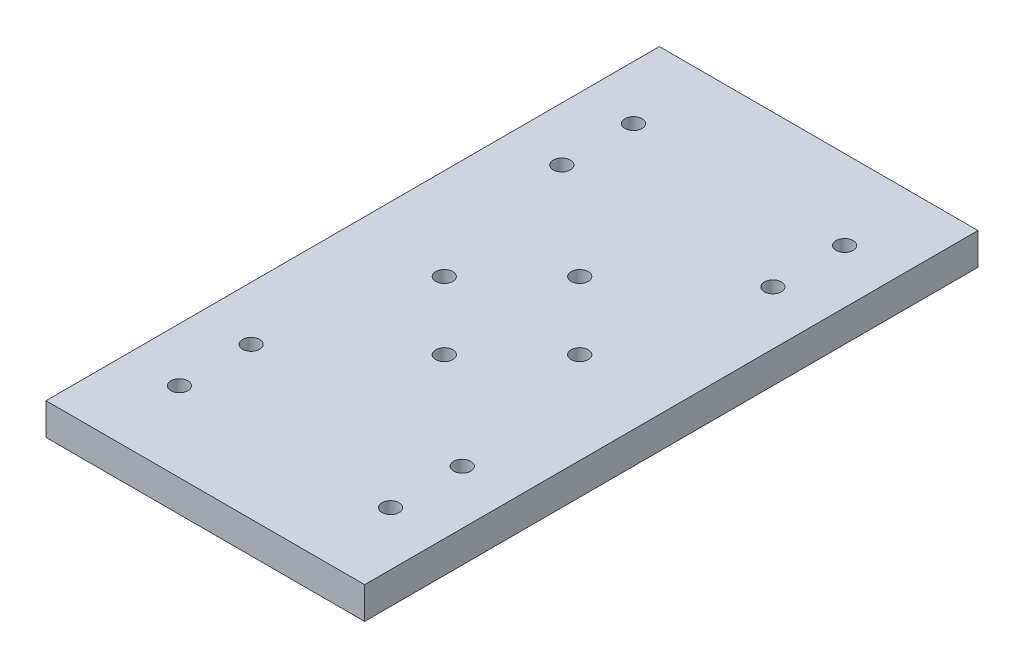
SolidWorks part; units mm, degrees
material "1060 Alloy"
ref_plane "Front" through (0, 0, 0) normal (0, 0, 1) x (1, 0, 0)
ref_plane "Top" through (0, 0, 0) normal (0, 1, 0) x (1, 0, 0)
ref_plane "Right" through (0, 0, 0) normal (1, 0, 0) x (0, 0, -1)
sketch "Sketch1" plane through (0, 0, 0) normal (0, 1, 0) x (1, 0, 0)
  line L0 (-83, 40) -> (-83, -40)
  line L1 (0, 0) -> (-83, 0)
  line L2 (0, 0) -> (0, 68.9891)
  line L3 (-40, 91.6515) -> (40, 91.6515)
  line L4 (-40, 91.6515) -> (-40, -91.6515)
  line L5 (-40, -91.6515) -> (40, -91.6515)
  line L6 (40, -91.6515) -> (40, 91.6515)
  line L7 (-40, 80.5) -> (40, 80.5)
  line L8 (-40, -80.5) -> (40, -80.5)
  circle A0 centre (0, 0) radius 92.1358
  circle A1 centre (0, 0) radius 100
  point P10 (-40, 80.5)
  dimension "D1" = 40
  dimension "D4" = 200
  dimension "D5" = 80
  dimension "D6" = 80.5
  dimension "D2" = 80
  dimension "D3" = 83
extrude "Boss-Extrude1" add sketch "Sketch1" along normal blind 8
hole_wizard "M4 Clearance Hole1" positions "Sketch3" profile "Sketch2" hole size "M4" standard "ISO" end condition through all
sketch "Sketch3" plane through (0, 8, 0) normal (0, 1, 0) x (1, 0, 0)
  line L0 (0, 0) -> (-28.0852, 0)
  line L1 (40, -80.5) -> (40, 80.5) construction
  line L2 (-40, 80.5) -> (40, 80.5) construction
  line L3 (-40, 80.5) -> (-40, -80.5) construction
  point P2 (-26.5, 57)
  point P4 (26.5, 57)
  point P22 (-26.5, 39)
  point P24 (26.5, 39)
  point P29 (26.5, -39)
  point P30 (-26.5, -39)
  point P31 (26.5, -57)
  point P32 (-26.5, -57)
  dimension "D1" = 18
  dimension "D2" = 18
  dimension "D3" = 23.5
  dimension "D4" = 13.5
  dimension "D5" = 13.5
  dimension "D6" = 23.5
sketch "Sketch2" plane through (-26.5, 8, -57) normal (1, 0, 0) x (0, 0, 1)
  line L0 (0, 0) -> (0, 8)
  line L1 (0, 8) -> (2.15, 8)
  line L2 (2.15, 8) -> (2.15, 0)
  line L5 (2.15, 0) -> (0, 0)
  line L11 (0, -6.35) -> (0, 107.95) construction
  dimension "Thru Hole Dia." = 4.3
  dimension "Thru Hole Depth" = 8
sketch "Sketch4" plane through (0, 8, 0) normal (0, 1, 0) x (1, 0, 0)
  line L0 (40, -80.5) -> (40, 80.5) construction
  line L1 (-40, 80.5) -> (40, 80.5)
  line L2 (-40, 80.5) -> (-40, 77)
  line L3 (-40, 77) -> (40, 77)
  line L4 (40, 80.5) -> (40, 77)
  line L5 (-40, 80.5) -> (-40, -80.5) construction
  line L6 (40, -80.5) -> (-40, -80.5)
  line L7 (40, -80.5) -> (40, -77)
  line L8 (40, -77) -> (-40, -77)
  line L9 (-40, -80.5) -> (-40, -77)
  dimension "D1" = 3.5
  dimension "D2" = 3.5
extrude "Cut-Extrude1" cut sketch "Sketch4" against normal blind 10
hole_wizard "M4 Clearance Hole2" positions "Sketch6" profile "Sketch5" hole size "M4" standard "ISO" end condition through all
sketch "Sketch6" plane through (0, 8, 0) normal (0, 1, 0) x (1, 0, 0)
  point P0 (-17, 0)
  point P8 (0, 17)
  point P9 (17, 0)
  point P10 (0, -17)
  dimension "D1" = 17
  dimension "D2" = 4
sketch "Sketch5" plane through (-17, 8, 0) normal (1, 0, 0) x (0, 0, 1)
  line L0 (0, 0) -> (0, 8)
  line L1 (0, 8) -> (2.15, 8)
  line L2 (2.15, 8) -> (2.15, 0)
  line L5 (2.15, 0) -> (0, 0)
  line L11 (0, -6.35) -> (0, 107.95) construction
  dimension "Thru Hole Dia." = 4.3
  dimension "Thru Hole Depth" = 8
